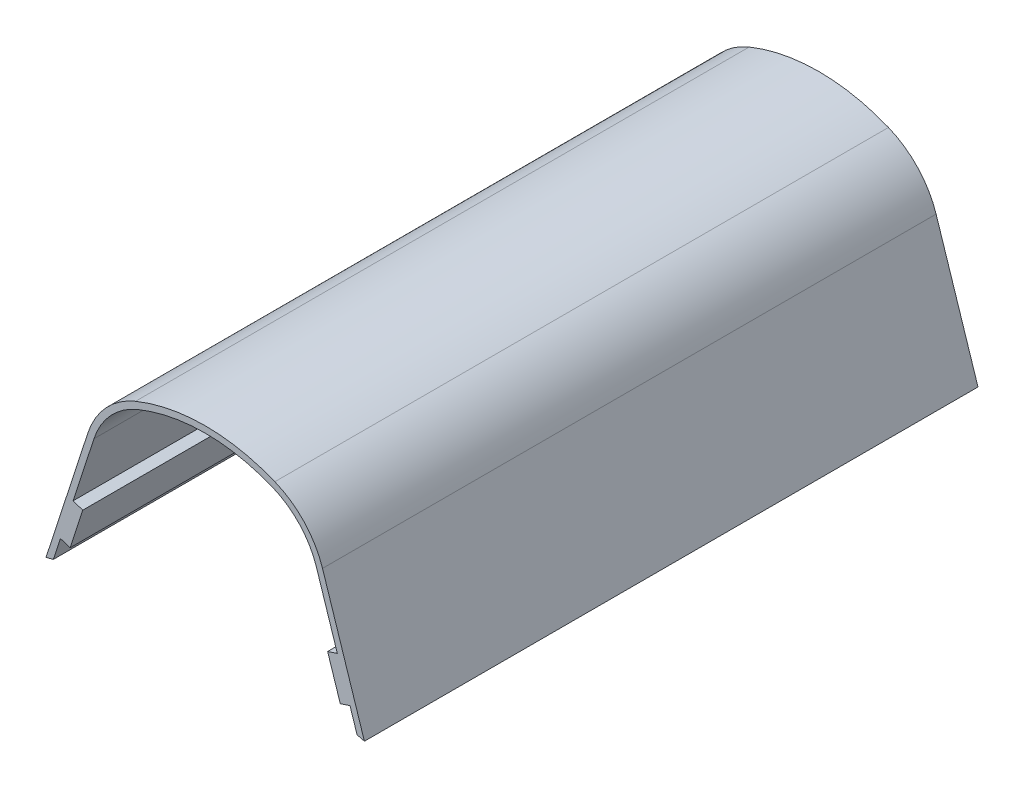
SolidWorks part; units mm, degrees
ref_plane "Front Plane" through (0, 0, 0) normal (0, 0, 1) x (1, 0, 0)
ref_plane "Top Plane" through (0, 0, 0) normal (0, 1, 0) x (1, 0, 0)
ref_plane "Right Plane" through (0, 0, 0) normal (1, 0, 0) x (0, 0, -1)
sketch "Sketch1" plane through (0, 0, 0) normal (0, 0, 1) x (1, 0, 0)
  line L0 (0, 0) -> (0, 324.652) construction
  line L1 (30.7076, 181.3003) -> (24.6961, 151.9943) construction
  line L2 (37.137, 149.4423) -> (40.6988, 166.8059) construction
  line L3 (-37.137, 149.4423) -> (-40.6988, 166.8059) construction
  line L4 (-30.7076, 181.3003) -> (-24.6961, 151.9943) construction
  line L5 (0, 0) -> (-38.8975, 189.6253) construction
  line L6 (27.6276, 178.6698) -> (37.137, 149.4423) construction
  line L7 (0, 0) -> (38.8975, 189.6253) construction
  line L12 (30.2004, 175.8931) -> (45.4337, 129.0731) construction
  line L13 (-27.6276, 178.6698) -> (-37.137, 149.4423) construction
  line L14 (-30.2004, 175.8931) -> (-45.4337, 129.0731) construction
  line L22 (37.7172, 147.659) -> (35.9655, 153.043)
  line L34 (-37.7172, 147.659) -> (-35.9655, 153.043)
  line L39 (-30.4067, 161.9187) -> (-32.822, 162.7045)
  line L40 (-30.4067, 161.9187) -> (-33.5501, 152.2572)
  line L41 (-33.5501, 152.2572) -> (-35.9655, 153.043)
  line L42 (33.5501, 152.2572) -> (35.9655, 153.043)
  line L43 (30.4067, 161.9187) -> (33.5501, 152.2572)
  line L44 (30.4067, 161.9187) -> (32.822, 162.7045)
  line L45 (-32.822, 162.7045) -> (-32.0362, 165.1199)
  line L46 (32.822, 162.7045) -> (32.0362, 165.1199)
  line L51 (29.1372, 179.161) -> (39.5422, 147.1807)
  line L52 (27.6276, 178.6698) -> (32.0362, 165.1199)
  line L53 (-27.6276, 178.6698) -> (-32.0362, 165.1199)
  line L54 (-29.1372, 179.161) -> (-39.5422, 147.1807)
  circle A0 centre (0, 0) radius 152.4 construction
  circle A1 centre (9.5123, 172.7758) radius 12.7 construction
  circle A2 centre (9.5123, 172.7758) radius 19.05 construction
  circle A3 centre (-15.875, 171.9727) radius 6.35 construction
  circle A4 centre (-15.875, 171.9727) radius 12.7 construction
  circle A5 centre (0, 0) radius 153.9875 construction
  circle A8 centre (0, 149.4423) radius 44.248 construction
  circle A10 centre (0, 149.4423) radius 45.8355 construction
  circle A38 centre (15.875, 171.9727) radius 12.7 construction
  circle A39 centre (15.875, 171.9727) radius 6.35 construction
  arc A40 (-37.7172, 147.659) -> (-39.5422, 147.1807) centre (0, 0) ccw
  arc A41 (39.5422, 147.1807) -> (37.7172, 147.659) centre (0, 0) ccw
  arc A45 (16.7037, 190.4163) -> (-16.7037, 190.4163) centre (0, 149.4423) ccw
  arc A47 (27.6276, 178.6698) -> (16.7037, 190.4163) centre (9.5123, 172.7758) ccw
  arc A49 (17.303, 191.8864) -> (-17.303, 191.8864) centre (0, 149.4423) ccw
  arc A50 (29.1372, 179.161) -> (17.303, 191.8864) centre (9.5123, 172.7758) ccw
  arc A51 (-29.1372, 179.161) -> (-17.303, 191.8864) centre (-9.5123, 172.7758) cw
  arc A52 (-27.6276, 178.6698) -> (-16.7037, 190.4163) centre (-9.5123, 172.7758) cw
  dimension "D1" = 304.8
  dimension "D2" = 25.4
  dimension "D3" = 15.875
  dimension "D4" = 38.1
  dimension "D5" = 12.7
  dimension "D6" = 9.5123
  dimension "D8" = 307.975
  dimension "D7" = 3.7866
  dimension "D11" = 88.496
  dimension "D12" = 91.671
  dimension "D13" = 1.5875
  dimension "D14" = 20.6375
  dimension "D9" = 6.35
  dimension "D10" = 6.35
  dimension "D15" = 2.54
  dimension "D16" = 10.16
  dimension "D17" = 2.54
extrude "Boss-Extrude2" add sketch "Sketch1" along normal blind 152.4
